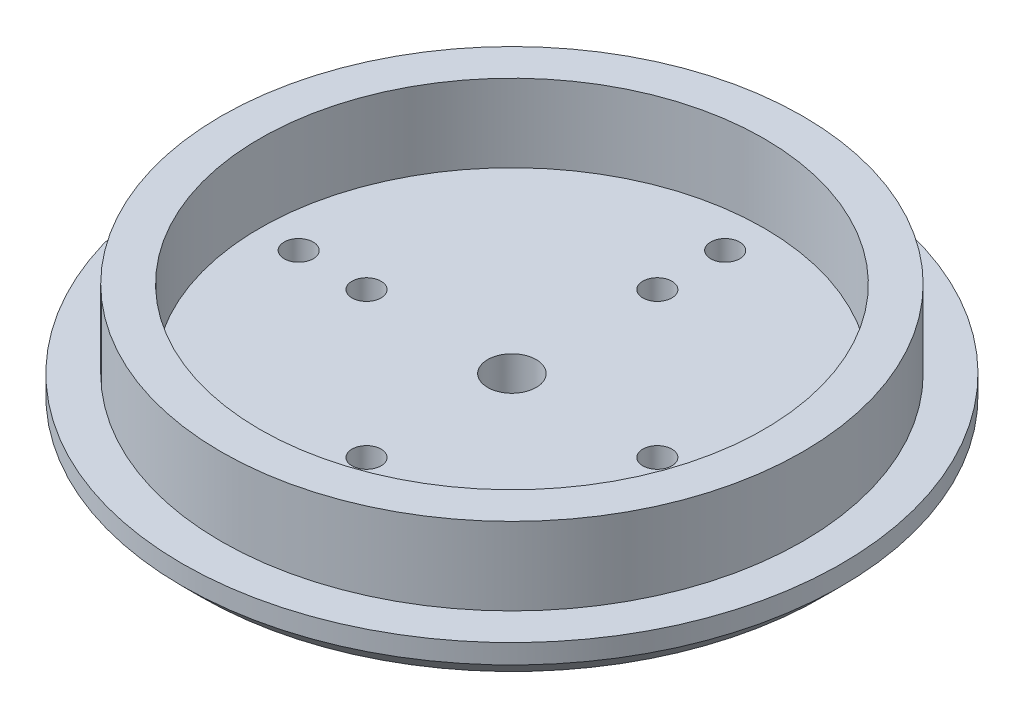
SolidWorks part; units mm, degrees
ref_plane "前视基准面" through (0, 0, 0) normal (0, 0, 1) x (1, 0, 0)
ref_plane "上视基准面" through (0, 0, 0) normal (0, 1, 0) x (1, 0, 0)
ref_plane "右视基准面" through (0, 0, 0) normal (1, 0, 0) x (0, 0, -1)
sketch "草图1" plane through (0, 0, 0) normal (0, 1, 0) x (1, 0, 0)
  circle A0 centre (0, 0) radius 34
  dimension "D1" = 68
extrude "凸台-拉伸1" add sketch "草图1" along normal blind 4
sketch "草图2" plane through (0, 4, 0) normal (0, 1, 0) x (1, 0, 0)
  circle A0 centre (0, 0) radius 30
  circle A1 centre (0, 0) radius 26
  dimension "D1" = 60
  dimension "D2" = 52
extrude "凸台-拉伸2" add sketch "草图2" along normal blind 8
sketch "草图3" plane through (0, 0, 0) normal (0, -1, 0) x (1, 0, 0)
  circle A0 centre (0, 0) radius 2.5
  circle A1 centre (0, 0) radius 15 construction
  circle A2 centre (0, 0) radius 22 construction
  circle A3 centre (0, 15) radius 1.5
  circle A4 centre (0, 22) radius 1.5
  circle A5 centre (15, 0) radius 1.5
  circle A6 centre (22, 0) radius 1.5
  circle A7 centre (0, -15) radius 1.5
  circle A8 centre (0, -22) radius 1.5
  circle A9 centre (-15, 0) radius 1.5
  circle A10 centre (-22, 0) radius 1.5
  point P24 (0, 0)
  dimension "D1" = 44
  dimension "D2" = 30
  dimension "D3" = 5
  dimension "D4" = 3
  dimension "D5" = 3
  dimension "D6" = 4
extrude "切除-拉伸1" cut sketch "草图3" against normal through all
sketch "草图4" plane through (0, 0, 0) normal (0, -1, 0) x (1, 0, 0)
  circle A0 centre (0, 0) radius 6
  circle A1 centre (0, 0) radius 2.5
  dimension "D1" = 12
extrude "凸台-拉伸3" add sketch "草图4" along normal blind 1
chamfer "倒角1" distance 2 angle 45 1 edges at (0, 0, 34)
sketch "草图5" plane through (0, 0, 0) normal (0, -1, 0) x (1, 0, 0)
  line L0 (0, 0) -> (-22.6274, -22.6274) construction
  line L1 (0, 0) -> (0, -32) construction
  line L2 (-18.7383, -18.7383) -> (-16.617, -16.617) construction
  line L3 (-19.4454, -18.0312) -> (-17.3241, -15.9099)
  line L4 (-18.0312, -19.4454) -> (-15.9099, -17.3241)
  line L5 (-18.3848, -16.9706) -> (-16.9706, -18.3848) construction
  line L6 (-13.7886, -19.4454) -> (-15.9099, -21.5668) construction
  line L7 (-13.0815, -20.1525) -> (-15.2028, -22.2739)
  line L8 (-14.4957, -18.7383) -> (-16.617, -20.8597)
  line L9 (-17.6777, -17.6777) -> (-14.8492, -20.5061) construction
  line L10 (-19.4454, -13.7886) -> (-21.5668, -15.9099) construction
  line L11 (-20.1525, -13.0815) -> (-22.2739, -15.2028)
  line L12 (-18.7383, -14.4957) -> (-20.8597, -16.617)
  circle A0 centre (0, 0) radius 32 construction
  arc A1 (-19.4454, -18.0312) -> (-18.0312, -19.4454) centre (-18.7383, -18.7383) ccw
  arc A2 (-15.9099, -17.3241) -> (-17.3241, -15.9099) centre (-16.617, -16.617) ccw
  arc A3 (-13.0815, -20.1525) -> (-14.4957, -18.7383) centre (-13.7886, -19.4454) ccw
  arc A4 (-16.617, -20.8597) -> (-15.2028, -22.2739) centre (-15.9099, -21.5668) ccw
  arc A5 (-20.1525, -13.0815) -> (-18.7383, -14.4957) centre (-19.4454, -13.7886) cw
  arc A6 (-20.8597, -16.617) -> (-22.2739, -15.2028) centre (-21.5668, -15.9099) cw
  point P8 (-17.6777, -17.6777)
  point P17 (-14.8492, -20.5061)
  point P26 (-20.5061, -14.8492)
  dimension "D1" = 45
  dimension "D2" = 2
  dimension "D3" = 3
  dimension "D4" = 25
  dimension "D5" = 4
extrude "凸台-拉伸4" add sketch "草图5" along normal blind 1
